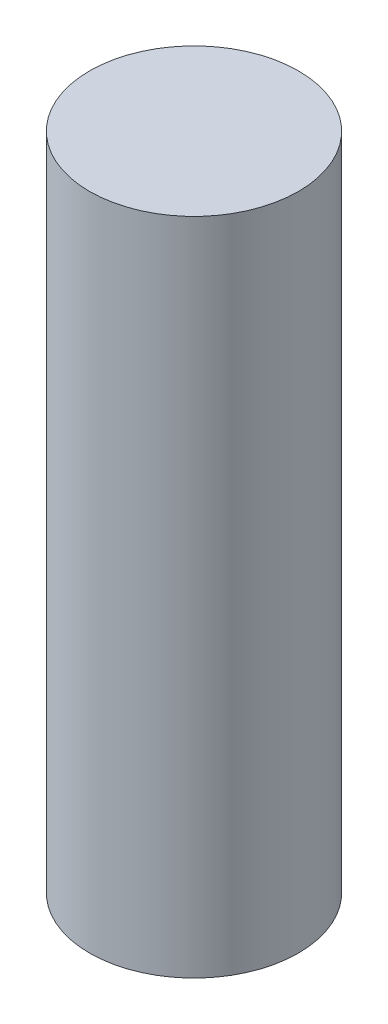
SolidWorks part; units mm, degrees
ref_plane "Front Plane" through (0, 0, 0) normal (0, 0, 1) x (1, 0, 0)
ref_plane "Top Plane" through (0, 0, 0) normal (0, 1, 0) x (1, 0, 0)
ref_plane "Right Plane" through (0, 0, 0) normal (1, 0, 0) x (0, 0, -1)
sketch "Sketch1" plane through (0, 0, 0) normal (0, 1, 0) x (1, 0, 0)
  circle A0 centre (0, 0) radius 19
  dimension "D1" = 38
extrude "Boss-Extrude1" add sketch "Sketch1" along normal blind 120
